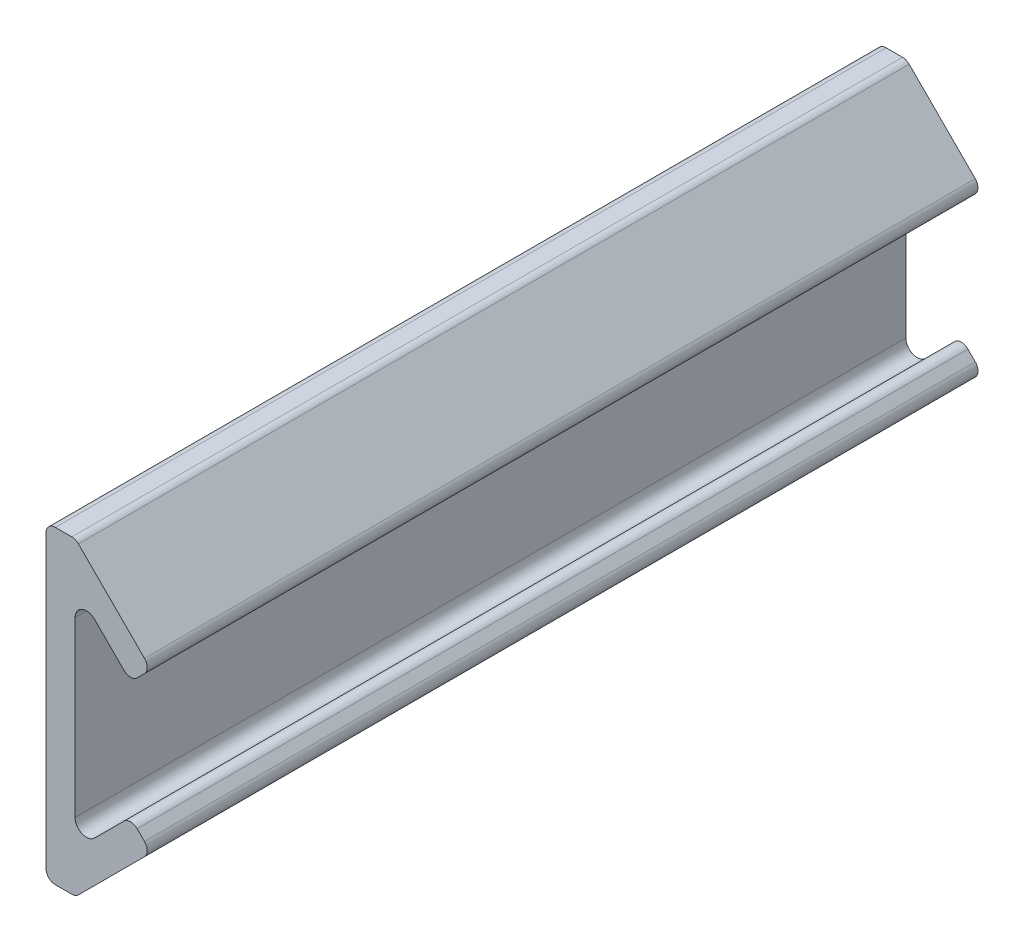
SolidWorks part; units mm, degrees
ref_plane "Plan de face" through (0, 0, 0) normal (0, 0, 1) x (1, 0, 0)
ref_plane "Plan de dessus" through (0, 0, 0) normal (0, 1, 0) x (1, 0, 0)
ref_plane "Plan de droite" through (0, 0, 0) normal (1, 0, 0) x (0, 0, -1)
sketch "Esquisse1" plane through (0, 0, 0) normal (0, 0, 1) x (1, 0, 0)
  line L0 (3.2929, 14.7071) -> (9.6569, 8.3431)
  line L1 (0, 0) -> (3, 0)
  line L2 (0, -14) -> (0, 14)
  line L3 (1, 15) -> (2.5858, 15)
  line L4 (3, -8.3431) -> (3, 8.3431)
  line L5 (10.364, 7.636) -> (3, 15)
  line L6 (9.6569, 6.9289) -> (8.9497, 6.2218)
  line L7 (3, 15) -> (2.9365, 14.9365)
  line L8 (7.5355, 6.2218) -> (4.7071, 9.0503)
  line L9 (7.5355, -6.2218) -> (4.7071, -9.0503)
  line L10 (9.6569, -6.9289) -> (8.9497, -6.2218)
  line L11 (3.2929, -14.7071) -> (9.6569, -8.3431)
  line L12 (1, -15) -> (2.5858, -15)
  line L13 (3.2222, -14.6364) -> (9.5861, -8.2724)
  line L14 (9.5861, -6.9996) -> (8.879, -6.2925)
  line L15 (7.6062, -6.2925) -> (4.7778, -9.121)
  line L16 (2.9, -8.3431) -> (2.9, 8.3431)
  line L17 (7.6062, 6.2925) -> (4.7778, 9.121)
  line L18 (9.5861, 6.9996) -> (8.879, 6.2925)
  line L19 (3.2222, 14.6364) -> (9.5861, 8.2724)
  line L20 (1, 14.9) -> (2.5858, 14.9)
  line L21 (0.1, -14) -> (0.1, 14)
  line L22 (1, -14.9) -> (2.5858, -14.9)
  arc A0 (3, 8.3431) -> (4.7071, 9.0503) centre (4, 8.3431) cw
  arc A1 (8.9497, 6.2218) -> (7.5355, 6.2218) centre (8.2426, 6.9289) cw
  arc A2 (9.6569, 8.3431) -> (9.6569, 6.9289) centre (8.9497, 7.636) cw
  arc A3 (3.2929, 14.7071) -> (2.5858, 15) centre (2.5858, 14) ccw
  arc A4 (1, 15) -> (0, 14) centre (1, 14) ccw
  arc A5 (3, -8.3431) -> (4.7071, -9.0503) centre (4, -8.3431) ccw
  arc A6 (8.9497, -6.2218) -> (7.5355, -6.2218) centre (8.2426, -6.9289) ccw
  arc A7 (9.6569, -8.3431) -> (9.6569, -6.9289) centre (8.9497, -7.636) ccw
  arc A8 (3.2929, -14.7071) -> (2.5858, -15) centre (2.5858, -14) cw
  arc A9 (1, -15) -> (0, -14) centre (1, -14) cw
  arc A10 (9.5861, -8.2724) -> (9.5861, -6.9996) centre (8.9497, -7.636) ccw
  arc A11 (8.879, -6.2925) -> (7.6062, -6.2925) centre (8.2426, -6.9289) ccw
  arc A12 (2.9, -8.3431) -> (4.7778, -9.121) centre (4, -8.3431) ccw
  arc A13 (2.9, 8.3431) -> (4.7778, 9.121) centre (4, 8.3431) cw
  arc A14 (8.879, 6.2925) -> (7.6062, 6.2925) centre (8.2426, 6.9289) cw
  arc A15 (9.5861, 8.2724) -> (9.5861, 6.9996) centre (8.9497, 7.636) cw
  arc A16 (3.2222, 14.6364) -> (2.5858, 14.9) centre (2.5858, 14) ccw
  arc A17 (1, 14.9) -> (0.1, 14) centre (1, 14) ccw
  arc A18 (1, -14.9) -> (0.1, -14) centre (1, -14) cw
  arc A19 (3.2222, -14.6364) -> (2.5858, -14.9) centre (2.5858, -14) cw
  point P13 (8.2426, 5.5147)
  point P22 (0, 15)
  dimension "D2" = 1
  dimension "D3" = 1
  dimension "D6" = 1
  dimension "D7" = 1
  dimension "D8" = 1
  dimension "D1" = 15
  dimension "D4" = 3
  dimension "D5" = 45
  dimension "D9" = 9
  dimension "D10" = 4
  dimension "D11" = 3
  dimension "D12" = 0.1
extrude "Boss.-Extru.1" add sketch "Esquisse1" along normal blind 80 contours A19 L13 A10 L14 A11 L15 A12 L16 L1 L21 A18 L22 | L20 A17 L21 L1 L16 A13 L17 A14 L18 A15 L19 A16
